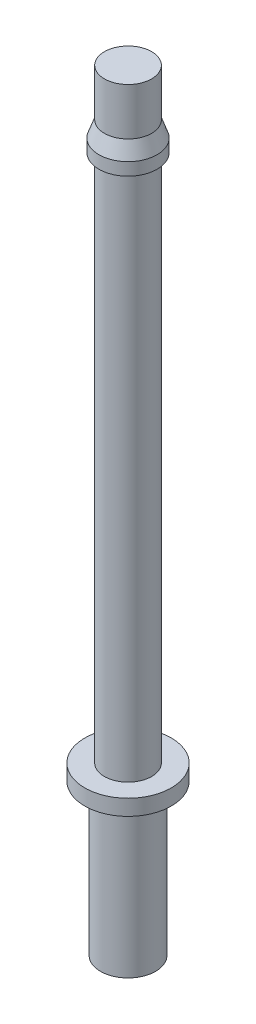
SolidWorks part; units mm, degrees
ref_plane "Front" through (0, 0, 0) normal (0, 0, 1) x (1, 0, 0)
ref_plane "Top" through (0, 0, 0) normal (0, 1, 0) x (1, 0, 0)
ref_plane "Right" through (0, 0, 0) normal (1, 0, 0) x (0, 0, -1)
sketch "Sketch1" plane through (0, 0, 0) normal (0, 0, 1) x (1, 0, 0)
  line L0 (0, 0) -> (0, 78.5431) construction
  line L1 (0, 0) -> (1.75, 0)
  line L2 (1.75, 0) -> (1.75, 9.6)
  line L3 (1.75, 9.6) -> (2.75, 9.6)
  line L4 (2.75, 9.6) -> (2.75, 10.6)
  line L5 (2.75, 10.6) -> (1.5, 10.6)
  line L6 (1.5, 10.6) -> (1.5, 44.2)
  line L7 (1.5, 44.2) -> (1.85, 44.2)
  line L8 (1.85, 44.2) -> (1.85, 45)
  line L9 (1.85, 45) -> (1.5, 46)
  line L10 (1.5, 46) -> (1.5, 49)
  line L11 (1.5, 49) -> (0, 49)
  line L12 (0, 49) -> (0, 0)
  dimension "D1" = 3.5
  dimension "D2" = 9.6
  dimension "D3" = 1
  dimension "D4" = 5.5
  dimension "D5" = 49
  dimension "D6" = 3
  dimension "D7" = 3
  dimension "D8" = 4.8
  dimension "D9" = 3.7
  dimension "D10" = 3
  dimension "D11" = 0.8
revolve "Revolve1" add sketch "Sketch1" angle 360 about L0
